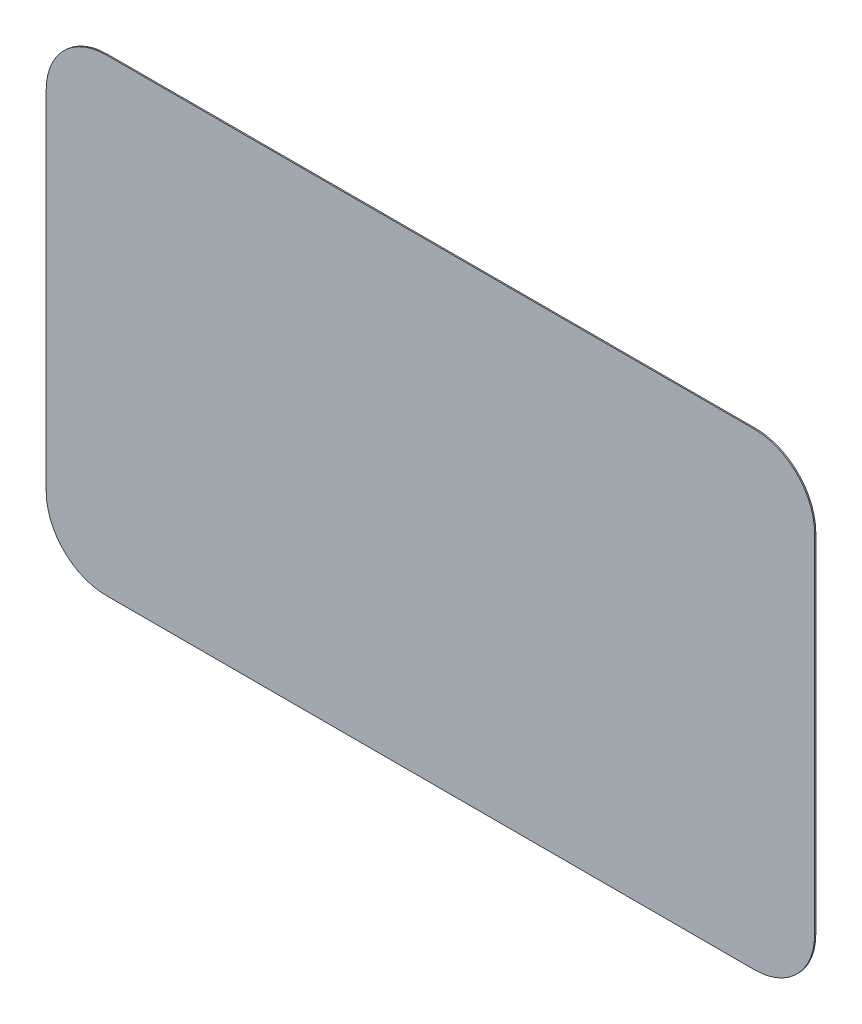
SolidWorks part; units mm, degrees
ref_plane "Front Plane" through (0, 0, 0) normal (0, 0, 1) x (1, 0, 0)
ref_plane "Top Plane" through (0, 0, 0) normal (0, 1, 0) x (1, 0, 0)
ref_plane "Right Plane" through (0, 0, 0) normal (1, 0, 0) x (0, 0, -1)
sketch "Sketch1" plane through (0, 0, 0) normal (0, 0, 1) x (1, 0, 0)
  line L4 (-135, -97.5) -> (135, -97.5)
  line L5 (160, -72.5) -> (160, 72.5)
  line L6 (135, 97.5) -> (-135, 97.5)
  line L7 (-160, 72.5) -> (-160, -72.5)
  line L8 (-135, -97.5) -> (135, -97.5)
  line L9 (160, -72.5) -> (160, 72.5)
  line L10 (135, 97.5) -> (-135, 97.5)
  line L11 (-160, 72.5) -> (-160, -72.5)
  arc A4 (-160, -72.5) -> (-135, -97.5) centre (-135, -72.5) ccw
  arc A5 (135, -97.5) -> (160, -72.5) centre (135, -72.5) ccw
  arc A6 (160, 72.5) -> (135, 97.5) centre (135, 72.5) ccw
  arc A7 (-135, 97.5) -> (-160, 72.5) centre (-135, 72.5) ccw
  arc A8 (-160, -72.5) -> (-135, -97.5) centre (-135, -72.5) ccw
  arc A9 (135, -97.5) -> (160, -72.5) centre (135, -72.5) ccw
  arc A10 (160, 72.5) -> (135, 97.5) centre (135, 72.5) ccw
  arc A11 (-135, 97.5) -> (-160, 72.5) centre (-135, 72.5) ccw
  dimension "D1" = 0
extrude "Boss-Extrude1" add sketch "Sketch1" along normal blind 0.5
sketch "Sketch3" plane through (0, 0, 0) normal (0, 0, -1) x (-1, 0, 0)
  line L0 (-135, -97.5) -> (-75, -97.5)
  line L1 (135, -97.5) -> (-135, -97.5) construction
  line L2 (-75, -97.5) -> (-75, -37.5)
  line L3 (-100, -12.5) -> (-160, -12.5)
  line L4 (-160, -72.5) -> (-160, 72.5) construction
  line L5 (-160, -12.5) -> (-160, -72.5)
  arc A1 (-160, -72.5) -> (-135, -97.5) centre (-135, -72.5) ccw construction
  arc A2 (-160, -72.5) -> (-135, -97.5) centre (-135, -72.5) ccw
  arc A3 (-75, -37.5) -> (-100, -12.5) centre (-100, -37.5) ccw
  dimension "D1" = 25
  dimension "D2" = 85
  dimension "D3" = 85
ref_plane "Plane1" through (0, 0, -69.5) normal (0, 0, 1) x (1, 0, 0)
sketch "Sketch4" plane through (0, 0, -69.5) normal (0, 0, 1) x (1, 0, 0)
  line L18 (153, -72.5) -> (153, -19.5)
  line L19 (82, -90.5) -> (135, -90.5)
  line L20 (82, -37.5) -> (82, -90.5)
  line L21 (153, -19.5) -> (100, -19.5)
  line L22 (153, -72.5) -> (153, -19.5)
  line L23 (82, -90.5) -> (135, -90.5)
  line L24 (82, -37.5) -> (82, -90.5)
  line L25 (153, -19.5) -> (100, -19.5)
  arc A9 (135, -90.5) -> (153, -72.5) centre (135, -72.5) ccw
  arc A10 (100, -19.5) -> (82, -37.5) centre (100, -37.5) ccw
  arc A11 (135, -90.5) -> (153, -72.5) centre (135, -72.5) ccw
  arc A12 (100, -19.5) -> (82, -37.5) centre (100, -37.5) ccw
  dimension "D1" = 7
loft "Loft1" add profiles "Sketch3", "Sketch4"
fillet "Fillet1" radius 20 2 edges
fillet "Fillet2" radius 5 7 edges at (85.8382, -91.1008, -63.5349) (153.4376, -25.1402, -65.1551)
sketch "Sketch5" plane through (0, 0, 0) normal (0, 1, 0) x (1, 0, 0)
  line L0 (135, 0) -> (-135, 0) construction
  line L1 (75, 69.5) -> (160, 69.5)
  line L2 (75, 69.5) -> (75, 0)
  line L3 (75, 0) -> (160, 0)
  line L4 (160, 69.5) -> (160, 0)
  line L5 (100.0868, 69.5) -> (148.4783, 69.5) construction
  line L6 (80.1875, 51.5042) -> (75, 0) construction
  line L7 (100, 0) -> (75, 0) construction
extrude "Cut-Extrude1" cut sketch "Sketch5" against normal through all
